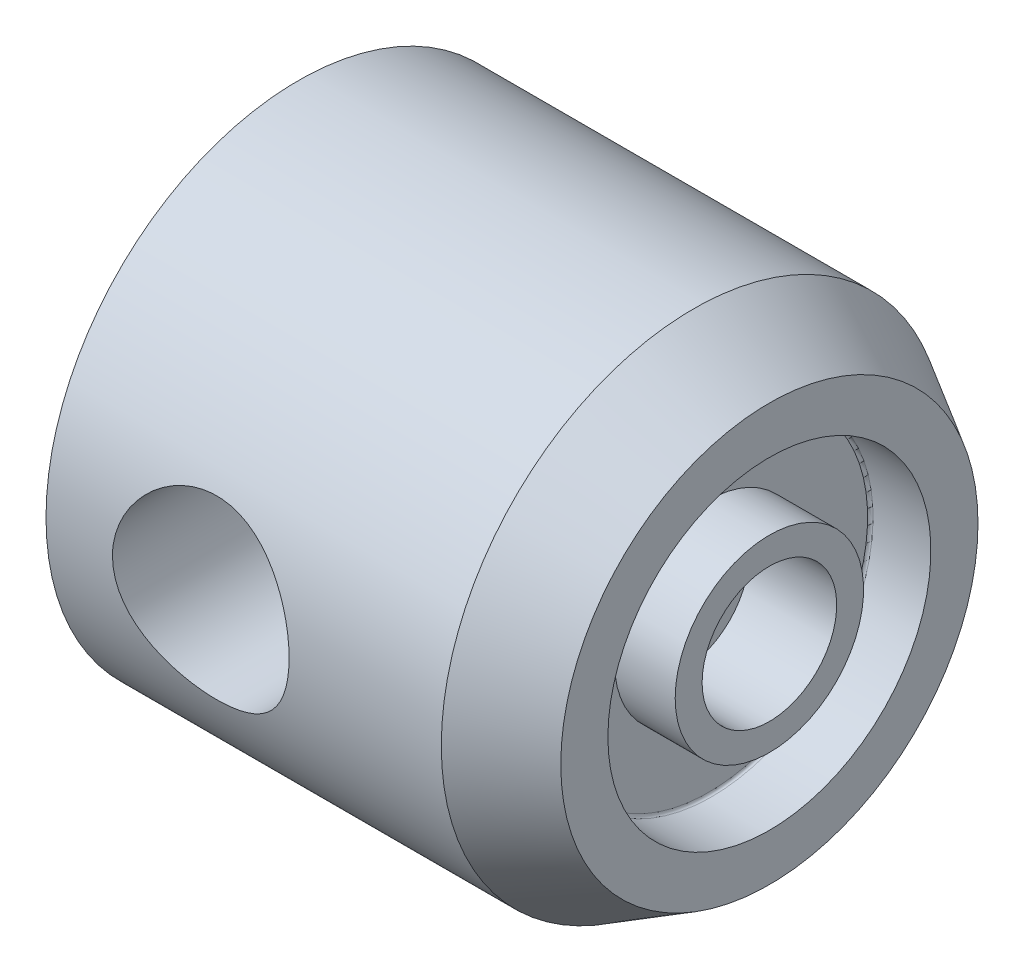
SolidWorks part; units mm, degrees
revolve "Cut-Revolve3" cut sketch "Sketch5" angle 360 about L0
sketch "Sketch5" plane through (24, 0, 0) normal (1, 0, 0) x (0, 0, -1)
  line L0 (0, 0) -> (22.3671, -47.9664) construction
  line L1 (0, 0) -> (0, -59.5073) construction
  line L2 (16.0595, -34.4397) -> (25.1226, -30.2135)
  line L3 (25.1226, -30.2135) -> (24.2773, -28.4009)
  line L4 (24.2773, -28.4009) -> (20.5615, -30.1336)
  line L5 (20.5615, -30.1336) -> (2.8115, 7.9313)
  line L6 (2.8115, 7.9313) -> (-3.9753, 8.5251)
  line L7 (16.0595, -34.4397) -> (-3.9753, 8.5251)
  dimension "D1" = 25
  dimension "D2" = 44
  dimension "D3" = 2
  dimension "D4" = 11.8
  dimension "D5" = 20
  dimension "D6" = 38
  dimension "D7" = 60
cosmetic thread "Cosmetic Thread6"
ref_plane "Front" through (0, 0, 0) normal (0, 0, 1) x (1, 0, 0)
ref_plane "Top" through (0, 0, 0) normal (0, 1, 0) x (1, 0, 0)
ref_plane "Right" through (0, 0, 0) normal (1, 0, 0) x (0, 0, -1)
sketch "Sketch1" plane through (0, 0, 0) normal (0, 0, 1) x (1, 0, 0)
  line L0 (-65.5921, 0) -> (115.6352, 0) construction
  line L1 (0, -45.0387) -> (0, 68.273) construction
  line L2 (-23, 0) -> (-23, 37.5)
  line L3 (-23, 37.5) -> (35.7417, 37.5)
  line L4 (35.7417, 37.5) -> (47, 31)
  line L5 (47, 31) -> (47, 24)
  line L6 (47, 10) -> (34, 10)
  line L7 (34, 10) -> (34, 6)
  line L8 (34, 6) -> (25, 6)
  line L9 (25, 6) -> (21.5359, 0)
  line L10 (47, 24) -> (38, 24)
  line L11 (38, 24) -> (38, 14)
  line L12 (38, 14) -> (47, 14)
  line L13 (47, 14) -> (47, 10)
  line L14 (-23, 0) -> (21.5359, 0)
  circle A0 centre (0, 0) radius 13.5 construction
  dimension "D1" = 27
  dimension "D2" = 47
  dimension "D3" = 70
  dimension "D4" = 75
  dimension "D5" = 62
  dimension "D6" = 48
  dimension "D7" = 28
  dimension "D8" = 20
  dimension "D9" = 12
  dimension "D10" = 60
  dimension "D11" = 9
  dimension "D12" = 30
  dimension "D13" = 13
  dimension "D14" = 22
revolve "Base-Revolve" add sketch "Sketch1" angle 360 about L0
sketch "Sketch2" plane through (0, 0, 0) normal (0, 0, 1) x (1, 0, 0)
  line L0 (-29.4272, 24) -> (47, 24) construction
  line L1 (47, 31) -> (47, -31) construction
  line L2 (-23, 36) -> (-21.5, 36)
  line L3 (-23, 37.5) -> (-23, -37.5) construction
  line L4 (-21.5, 36) -> (-21.5, 31.65)
  line L5 (-21.5, 31.65) -> (39, 31.65)
  line L6 (39, 31.65) -> (43.4167, 24)
  line L7 (-23, 36) -> (-23, 24)
  line L8 (43.4167, 24) -> (-23, 24)
  dimension "D1" = 24
  dimension "D2" = 7.65
  dimension "D3" = 12
  dimension "D4" = 62
  dimension "D5" = 60
  dimension "D6" = 1.5
revolve "Cut-Revolve1" cut sketch "Sketch2" angle 360 about L0
cosmetic thread "Cosmetic Thread5"
sketch "Sketch3" plane through (0, 0, 0) normal (0, 0, 1) x (1, 0, 0)
  line L0 (-27.4404, -24) -> (70.0762, -24) construction
  line L1 (-23, -36) -> (-21.5, -36)
  line L2 (-23, 37.5) -> (-23, -37.5) construction
  line L3 (-21.5, -36) -> (-21.5, -31.65)
  line L4 (-21.5, -31.65) -> (29, -31.65)
  line L5 (29, -31.65) -> (33.4167, -24)
  line L6 (-23, -36) -> (-23, -24)
  line L7 (33.4167, -24) -> (-23, -24)
  dimension "D1" = 24
  dimension "D2" = 1.5
  dimension "D3" = 52
  dimension "D4" = 7.65
  dimension "D5" = 60
  dimension "D6" = 12
revolve "Cut-Revolve2" cut sketch "Sketch3" angle 360 about L0
cosmetic thread "Cosmetic Thread4"
sketch "Sketch4" plane through (0, 0, 0) normal (0, 0, 1) x (1, 0, 0)
  circle A0 centre (0, 0) radius 13.125
  dimension "D1" = 26.25
extrude "Cut-Extrude1" cut sketch "Sketch4" against normal mid plane 90
ref_plane "Plane4" through (24, 0, 0) normal (1, 0, 0) x (0, 0, -1)
fillet "Fillet1" radius 0.4 1 edges at (38, -24, 0)
